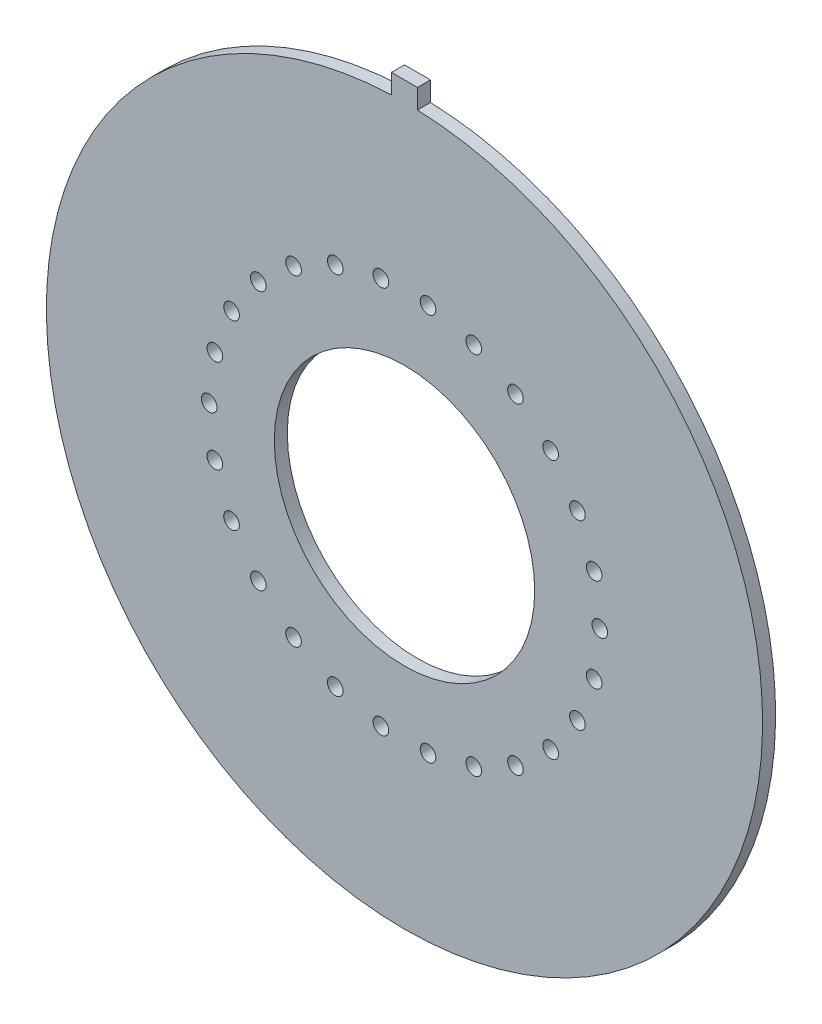
SolidWorks part; units mm, degrees
material "ABS"
ref_plane "Front Plane" through (0, 0, 0) normal (0, 0, 1) x (1, 0, 0)
ref_plane "Top Plane" through (0, 0, 0) normal (0, 1, 0) x (1, 0, 0)
ref_plane "Right Plane" through (0, 0, 0) normal (1, 0, 0) x (0, 0, -1)
sketch "PCB dimension" plane through (0, 0, 0) normal (0, 0, 1) x (1, 0, 0)
  line L0 (0, 0) -> (0, 42.7396) construction
  line L1 (-1, 27.4818) -> (-1, 28.9818)
  line L2 (-1, 28.9818) -> (1, 28.9818)
  line L3 (1, 28.9818) -> (1, 27.4818)
  line L4 (0, 0) -> (40.2767, 0) construction
  line L5 (0, 0) -> (37.5544, 0) construction
  arc A0 (-1, 27.4818) -> (1, 27.4818) centre (0, 0) ccw
  circle A1 centre (15, 0) radius 0.6
  circle A2 centre (14.5641, -3.5897) radius 0.6
  circle A3 centre (13.2818, -6.9708) radius 0.6
  circle A4 centre (11.2277, -9.9468) radius 0.6
  circle A5 centre (8.521, -12.3448) radius 0.6
  circle A6 centre (5.3191, -14.0252) radius 0.6
  circle A7 centre (1.8081, -14.8906) radius 0.6
  circle A8 centre (-1.8081, -14.8906) radius 0.6
  circle A9 centre (-5.3191, -14.0252) radius 0.6
  circle A10 centre (-8.521, -12.3448) radius 0.6
  circle A11 centre (-11.2277, -9.9468) radius 0.6
  circle A12 centre (-13.2818, -6.9708) radius 0.6
  circle A13 centre (-14.5641, -3.5897) radius 0.6
  circle A14 centre (-15, 0) radius 0.6
  circle A15 centre (-14.5641, 3.5897) radius 0.6
  circle A16 centre (-13.2818, 6.9708) radius 0.6
  circle A17 centre (-11.2277, 9.9468) radius 0.6
  circle A18 centre (-8.521, 12.3448) radius 0.6
  circle A19 centre (-5.3191, 14.0252) radius 0.6
  circle A20 centre (-1.8081, 14.8906) radius 0.6
  circle A21 centre (1.8081, 14.8906) radius 0.6
  circle A22 centre (5.3191, 14.0252) radius 0.6
  circle A23 centre (8.521, 12.3448) radius 0.6
  circle A24 centre (11.2277, 9.9468) radius 0.6
  circle A25 centre (13.2818, 6.9708) radius 0.6
  circle A26 centre (14.5641, 3.5897) radius 0.6
  circle A27 centre (0, 0) radius 10
  point P6 (0, 28.9818)
  point P64 (0, 0)
  dimension "D1" = 55
  dimension "D5" = 1.2
  dimension "D8" = 20
  dimension "D2" = 1.5
  dimension "D3" = 2
  dimension "D4" = 0
  dimension "D6" = 15
  dimension "D7" = 26
extrude "Boss-Extrude1" add sketch "PCB dimension" along normal blind 1
